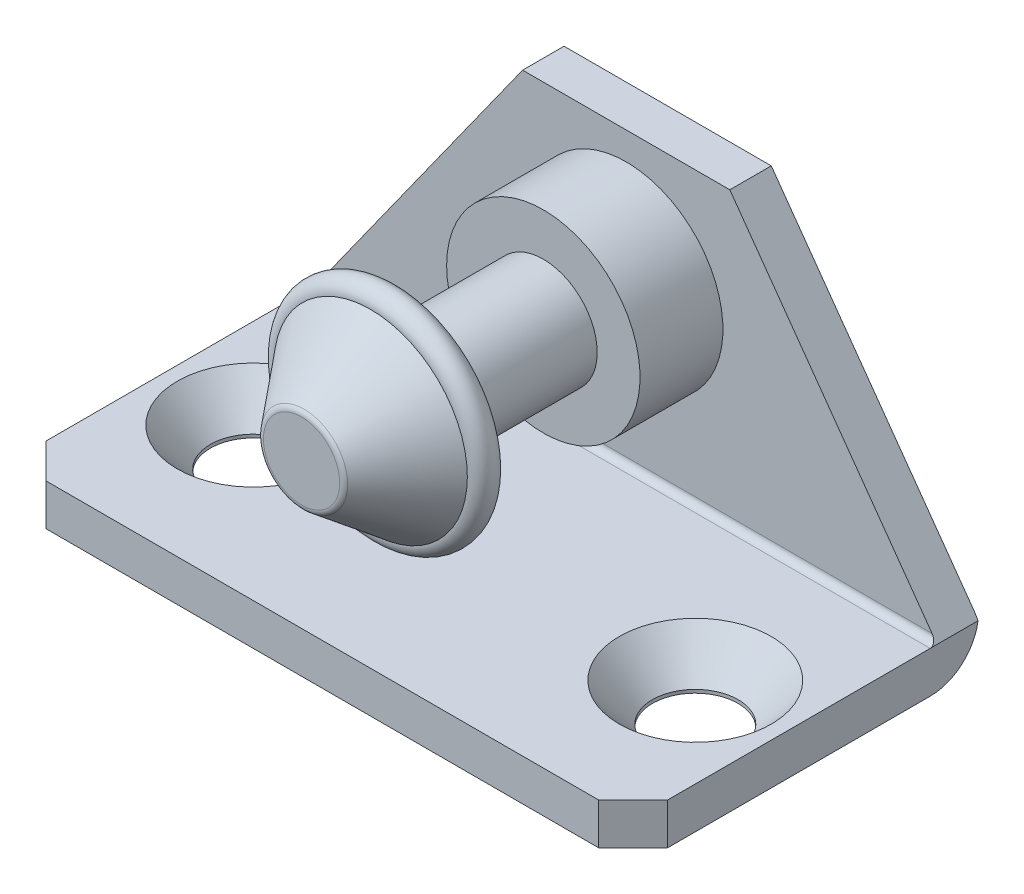
SolidWorks part; units mm, degrees
ref_plane "Front" through (0, 0, 0) normal (0, 0, 1) x (1, 0, 0)
ref_plane "Top" through (0, 0, 0) normal (0, 1, 0) x (1, 0, 0)
ref_plane "Right" through (0, 0, 0) normal (1, 0, 0) x (0, 0, -1)
sketch "Sketch1" plane through (0, 0, 0) normal (0, 1, 0) x (1, 0, 0)
  line L0 (-22.5, -25) -> (-22.5, 0)
  line L4 (22.5, 0) -> (22.5, -25)
  line L5 (22.5, -25) -> (-22.5, -25)
  line L6 (-22.5, 0) -> (22.5, 0)
  dimension "D1" = 45
  dimension "D2" = 25
extrude "Extrude1" add sketch "Sketch1" along normal blind 3
sketch "Sketch12" plane through (0, 0, 0) normal (0, 0, 1) x (1, 0, 0)
  line L0 (22.5, 3) -> (-22.5, 3) construction
  line L1 (22.5, 3) -> (7.5, 24)
  line L2 (7.5, 24) -> (-7.5, 24)
  line L3 (-7.5, 24) -> (-22.5, 3)
  line L4 (22.5, 0) -> (-22.5, 0) construction
  line L5 (22.5, 3) -> (22.5, 0) construction
  line L8 (22.5, 3) -> (-22.5, 3)
  line L9 (-22.5, 3) -> (-22.5, 0) construction
  dimension "D1" = 24
  dimension "D2" = 15
extrude "Extrude7" add sketch "Sketch12" along normal blind 3
fillet "Fillet3" radius 0.5 1 edges
fillet "Fillet4" radius 3.5 1 edges at (0, 0, 0)
hole_wizard "Hole1" positions "Sketch3" profile "Sketch2" legacy end condition through all
sketch "Sketch3" plane through (0, 3, 0) normal (0, 1, 0) x (-1, 0, 0)
  line L0 (-16, 14) -> (16, 14) construction
  line L6 (22.5, 25) -> (-22.5, 25) construction
  line L7 (0, 0) -> (0, 14) construction
  point P3 (-16, 14)
  point P5 (16, 14)
  dimension "D1" = 11
  dimension "D3" = 32
sketch "Sketch2" plane through (16, 3, 14) normal (1, 0, 0) x (0, 0, 1)
  line L0 (0, 0) -> (0, 3)
  line L1 (0, 3) -> (3.1, 3)
  line L2 (3.1, 3) -> (3.1, 2.7609)
  line L3 (3.1, 2.7609) -> (5.5, 0)
  line L4 (5.5, 0) -> (0, 0)
  line L5 (0, -6.4453) -> (0, 115.525) construction
  line L6 (-3.1, 2.7609) -> (-5.5, 0) construction
  dimension "Diameter" = 6.2
  dimension "Depth" = 3
  dimension "C-Sink Angle" = 82
  dimension "C-Sink Diameter" = 11
sketch "Sketch4" plane through (0, 0, 3) normal (0, 0, -1) x (-1, 0, 0)
  line L0 (22.5, 0) -> (-22.5, 0) construction
  line L4 (0, 0) -> (0, 15) construction
  circle A0 centre (0, 15) radius 7
  dimension "D1" = 15
  dimension "D2" = 14
extrude "Extrude2" add sketch "Sketch4" against normal blind 6
sketch "Sketch5" plane through (0, 0, 9) normal (0, 0, 1) x (-1, 0, 0)
  circle A0 centre (0, -15) radius 3.9
  dimension "D1" = 7.8
extrude "Extrude3" add sketch "Sketch5" along normal blind 10.5
sketch "Sketch6" plane through (0, 0, 19.5) normal (0, 0, 1) x (-1, 0, 0)
  circle A0 centre (0, -15) radius 3
  dimension "D1" = 6
extrude "Extrude4" add sketch "Sketch6" along normal blind 1.4
sketch "Sketch7" plane through (0, 0, 20.9) normal (0, 0, 1) x (-1, 0, 0)
  circle A0 centre (0, -15) radius 3.9 construction
  circle A1 centre (0, -15) radius 3.9
extrude "Extrude6" add sketch "Sketch7" along normal blind 3.1
ref_plane "Plane1" through (0, 15, 0) normal (0, 1, 0) x (1, 0, 0)
chamfer "Chamfer2" distance 1 angle 45 1 edges at (0, 11.1, 24)
sketch "Sketch8" plane through (0, 15, 0) normal (0, 1, 0) x (1, 0, 0)
  line L0 (0, -19.5) -> (-7, -19.5) construction
  line L1 (-7, -21.5) -> (-3, -26.5)
  line L2 (-3, -26.5) -> (0, -26.5)
  line L3 (0, -26.5) -> (0, -19.5) construction
  line L4 (0, -19.5) -> (0, 0) construction
  line L5 (-3.9, -19.5) -> (3.9, -19.5) construction
  line L6 (0, -26.5) -> (0, -23.85)
  line L7 (0, -23.85) -> (-4.125, -23.85)
  line L8 (-4.125, -23.85) -> (-4.125, -19.5)
  line L9 (-4.125, -19.5) -> (-7, -19.5)
  line L11 (-3.9, -24) -> (3.9, -24) construction
  line L12 (-3.9, -9) -> (-3.9, -19.5) construction
  line L13 (-3.9, -24) -> (3.9, -24) construction
  line L14 (-3.9, -9) -> (-3.9, -19.5) construction
  line L15 (-7, -9) -> (7, -9) construction
  line L16 (3.9, -19.5) -> (3.9, -9) construction
  line L17 (3.9, -19.5) -> (3.9, -9) construction
  arc A0 (-7, -19.5) -> (-7, -21.5) centre (-7, -20.5) ccw
  dimension "D2" = 2
  dimension "D1" = 16
  dimension "D3" = 7
  dimension "D4" = 6
  dimension "D5" = 4.125
  dimension "D6" = 0.15
  dimension "D7" = 15
  dimension "D8" = 7.8
revolve "Revolve1" add sketch "Sketch8" angle 360 about L4
fillet "Fillet1" radius 0.5 1 edges at (3, 15, 26.5)
sketch "Sketch9" plane through (0, 15, 0) normal (0, 1, 0) x (1, 0, 0)
  line L0 (-3.9, -24) -> (3.9, -24) construction
  line L1 (3.9, -20.9) -> (-3.9, -20.9) construction
  line L2 (-3, -19.5) -> (-3, -20.9) construction
  line L5 (3, -20.9) -> (3, -19.5) construction
  line L6 (-3.9, -24) -> (3.9, -24) construction
  line L7 (3.9, -20.9) -> (-3.9, -20.9) construction
  line L8 (-3, -19.5) -> (-3, -20.9) construction
  line L9 (-3.9, -20.9) -> (-3.9, -24) construction
  line L10 (3.9, -24) -> (3.9, -20.9) construction
  line L11 (3, -20.9) -> (3, -19.5) construction
chamfer "Chamfer1" distance 2.5 angle 45 2 edges at (22.5, 1.5, 25) (-22.5, 1.5, 25)
